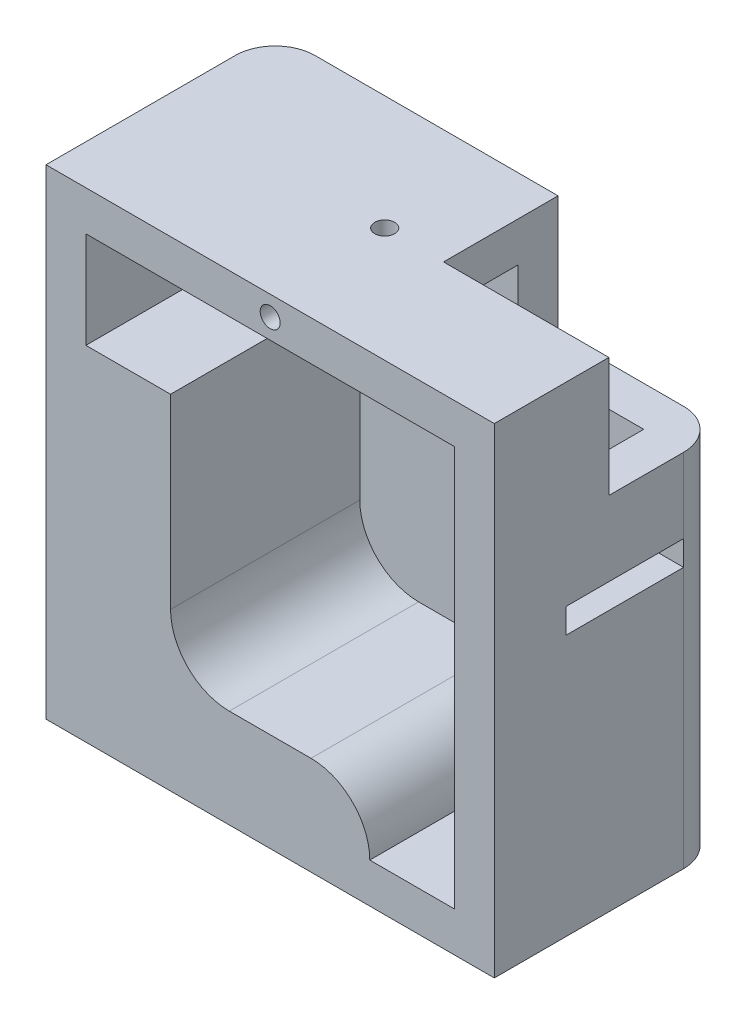
SolidWorks part; units mm, degrees
ref_plane "Alzado" through (0, 0, 0) normal (0, 0, 1) x (1, 0, 0)
ref_plane "Planta" through (0, 0, 0) normal (0, 1, 0) x (1, 0, 0)
ref_plane "Vista lateral" through (0, 0, 0) normal (1, 0, 0) x (0, 0, -1)
sketch "Croquis1" plane through (0, 0, 0) normal (1, 0, 0) x (0, 0, -1)
  line L0 (-5.9, 15.9) -> (5.9, 15.9) construction
  line L1 (5.9, 15.9) -> (5.9, -19.1) construction
  line L2 (5.9, -19.1) -> (-5.9, -19.1) construction
  line L3 (-5.9, -19.1) -> (-5.9, 15.9) construction
  line L4 (-2.3, 15.9) -> (-2.3, 19.1) construction
  line L5 (-2.3, 19.1) -> (2.3, 19.1) construction
  line L6 (2.3, 19.1) -> (2.3, 15.9) construction
  line L8 (11.5, 24.1) -> (-11.5, 24.1)
  line L9 (11.5, 24.1) -> (11.5, -24.1)
  line L10 (11.5, -24.1) -> (-11.5, -24.1)
  line L11 (-11.5, 24.1) -> (-11.5, -24.1)
  point P6 (0, 19.1)
  point P9 (0, 24.1)
  point P10 (11.5, 0)
  point P19 (0, -19.1)
  dimension "D1" = 11.8
  dimension "D2" = 35
  dimension "D3" = 3.6
  dimension "D4" = 5.9
  dimension "D5" = 3.2
  dimension "D6" = 23
  dimension "D7" = 5
  dimension "D8" = 5
extrude "Saliente-Extruir1" add sketch "Croquis1" along normal mid plane 45
shell "Vaciado1" thickness 4
sketch "Croquis2" plane through (0, 24.1, 0) normal (0, 1, 0) x (1, 0, 0)
  line L0 (-22.5, 0) -> (-18.5, 0) construction
  line L1 (-22.5, 11.5) -> (-22.5, -11.5) construction
  line L2 (-18.5, 0) -> (-13.8, 0) construction
  line L3 (-13.8, 0) -> (8.7, 0) construction
  line L4 (8.7, 0) -> (13.4, 0) construction
  line L5 (22.5, 11.5) -> (22.5, -11.5) construction
  line L6 (22.5, 0) -> (18.5, 0) construction
  line L7 (-13.8, 0) -> (-7.9, 0) construction
  line L8 (-22.5, 11.5) -> (-5.9, 11.5)
  line L9 (22.5, 11.5) -> (-22.5, 11.5) construction
  line L10 (-5.9, 11.5) -> (-5.9, 7.5)
  line L11 (-5.9, 7.5) -> (-18.5, 7.5)
  line L12 (-18.5, 7.5) -> (-18.5, 0)
  line L13 (-18.5, 0) -> (-22.5, 0)
  line L14 (-22.5, 0) -> (-22.5, 11.5)
  line L15 (0, -12.65) -> (0, 12.65) construction
  line L16 (18.5, 0) -> (22.5, 0)
  line L17 (18.5, 7.5) -> (18.5, 0)
  line L18 (5.9, 7.5) -> (18.5, 7.5)
  line L19 (5.9, 11.5) -> (5.9, 7.5)
  line L20 (22.5, 11.5) -> (5.9, 11.5)
  line L21 (22.5, 0) -> (22.5, 11.5)
  dimension "D2" = 4.7
  dimension "D3" = 22.5
  dimension "D4" = 4.7
  dimension "D5" = 5.9
  dimension "D6" = 2
  dimension "D7" = 4
  dimension "D8" = 4
extrude "Cortar-Extruir1" cut sketch "Croquis2" along normal blind 3.5 from offset 9.2 offset against normal yes
fillet "Redondeo1" radius 4 4 edges at (22.5, 21.25, -11.5) (22.5, -4.6, -11.5) (-22.5, -4.6, -11.5) (-22.5, 21.25, -11.5)
sketch "Croquis3" plane through (0, 0, 0) normal (1, 0, 0) x (0, 0, -1)
  line L0 (7.5, 14.9) -> (7.5, 10.9) construction
  line L1 (7.5, 14.9) -> (7.5, -24.1) construction
  line L2 (7.5, 10.9) -> (7.5, 4.6) construction
  line L4 (7.5, 4.6) -> (-4.3, 4.6)
  line L5 (7.5, 4.6) -> (7.5, 2.1)
  line L6 (7.5, 2.1) -> (-4.3, 2.1)
  line L7 (-4.3, 4.6) -> (-4.3, 2.1)
  dimension "D1" = 4
  dimension "D2" = 6.3
  dimension "D3" = 11.8
  dimension "D4" = 2.5
extrude "Cortar-Extruir2" cut sketch "Croquis3" against normal through all both and the other way through all
sketch "Croquis4" plane through (0, 24.1, 0) normal (0, 1, 0) x (1, 0, 0)
  circle A0 centre (0, 0) radius 1
  dimension "D1" = 2
extrude "Cortar-Extruir3" cut sketch "Croquis4" against normal up to next and the other way through all
sketch "Croquis5" plane through (0, 0, 11.5) normal (0, 0, 1) x (1, 0, 0)
  line L0 (0, 23.1) -> (0, 24.1) construction
  line L3 (0, 21.1) -> (0, 20.1) construction
  line L5 (18.5, 20.1) -> (-18.5, 20.1) construction
  line L6 (0, 24.1) -> (0, -24.1) construction
  line L7 (22.5, 24.1) -> (-22.5, 24.1) construction
  circle A0 centre (0, 22.1) radius 1
  dimension "D1" = 2
extrude "Cortar-Extruir4" cut sketch "Croquis5" against normal blind 5
sketch "Croquis6" plane through (0, 0, 11.5) normal (0, 0, 1) x (1, 0, 0)
  line L0 (-10, -20.1) -> (10, -20.1)
  line L1 (18.5, -20.1) -> (-18.5, -20.1) construction
  line L2 (4.1, -14.2) -> (-4.1, -14.2)
  arc A0 (10, -20.1) -> (4.1, -14.2) centre (4.1, -20.1) ccw
  arc A1 (-4.1, -14.2) -> (-10, -20.1) centre (-4.1, -20.1) ccw
  point P8 (0, -14.2)
  point P9 (0, -20.1)
  dimension "D2" = 20
  dimension "D1" = 5.9
extrude "Saliente-Extruir2" add sketch "Croquis6" against normal up to next
sketch "Croquis7" plane through (0, 24.1, 0) normal (0, 1, 0) x (1, 0, 0)
  line L0 (5.9, 7.5) -> (5.9, 0)
  line L1 (5.9, 0) -> (18.5, 0)
  line L6 (22.5, 0) -> (22.5, 7.5)
  line L7 (18.5, 11.5) -> (5.9, 11.5)
  line L8 (5.9, 11.5) -> (5.9, 7.5)
  line L9 (5.9, 7.5) -> (18.5, 7.5)
  line L10 (18.5, 7.5) -> (18.5, 0)
  line L11 (18.5, 0) -> (22.5, 0)
  line L12 (22.5, 0) -> (22.5, 7.5)
  line L13 (18.5, 11.5) -> (5.9, 11.5)
  line L14 (5.9, 11.5) -> (5.9, 7.5)
  line L15 (5.9, 7.5) -> (18.5, 7.5) construction
  line L16 (18.5, 7.5) -> (18.5, 0) construction
  line L17 (18.5, 0) -> (22.5, 0)
  arc A2 (22.5, 7.5) -> (18.5, 11.5) centre (18.5, 7.5) ccw
  arc A3 (22.5, 7.5) -> (18.5, 11.5) centre (18.5, 7.5) ccw
  dimension "D1" = 0
extrude "Cortar-Extruir5" cut sketch "Croquis7" along normal through all from offset 12 offset against normal yes
sketch "Croquis8" plane through (0, 0, 11.5) normal (0, 0, 1) x (1, 0, 0)
  line L0 (-18.5, -20.1) -> (-18.5, 10.4)
  line L1 (-18.5, 20.1) -> (-18.5, -20.1) construction
  line L2 (-18.5, 10.4) -> (-10, 10.4)
  line L3 (-10, 10.4) -> (-10, -8.3)
  line L5 (-10, -20.1) -> (-18.5, -20.1)
  arc A0 (-4.1, -14.2) -> (-10, -20.1) centre (-4.1, -20.1) ccw construction
  arc A2 (-4.1, -14.2) -> (-10, -8.3) centre (-4.1, -8.3) cw
  arc A3 (-4.1, -14.2) -> (-10, -20.1) centre (-4.1, -20.1) ccw construction
  arc A4 (-4.1, -14.2) -> (-10, -20.1) centre (-4.1, -20.1) ccw
  point P8 (0, 0)
  point P9 (0, 0)
  point P13 (-10, -8.3)
  point P14 (0, 0)
  point P15 (-4.0492, -14.2)
  dimension "D1" = 30.5
extrude "Saliente-Extruir3" add sketch "Croquis8" against normal up to next
